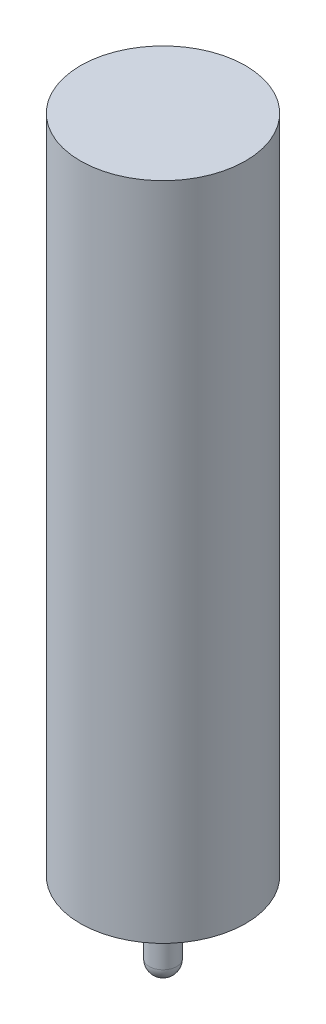
SolidWorks part; units mm, degrees
material "合金鋼 (SS)"
ref_plane "正面" through (0, 0, 0) normal (0, 0, 1) x (1, 0, 0)
ref_plane "平面" through (0, 0, 0) normal (0, 1, 0) x (1, 0, 0)
ref_plane "右側面" through (0, 0, 0) normal (1, 0, 0) x (0, 0, -1)
sketch "ｽｹｯﾁ1" plane through (0, 0, 0) normal (0, 1, 0) x (1, 0, 0)
  circle A0 centre (0, 0) radius 1.5
extrude "ﾎﾞｽ - 押し出し2" add sketch "ｽｹｯﾁ1" along normal blind 24
sketch "ｽｹｯﾁ3" plane through (0, 0, 0) normal (0, -1, 0) x (1, 0, 0)
  circle A0 centre (0, 0) radius 0.5
extrude "ﾎﾞｽ - 押し出し3" add sketch "ｽｹｯﾁ3" along normal blind 3.1
fillet "ﾌｨﾚｯﾄ1" radius 0.5 1 edges at (0, -3.1, -0.5)
sketch "ｽｹｯﾁ4" plane through (0, 24, 0) normal (0, 1, 0) x (1, 0, 0)
  circle A0 centre (0, 0) radius 3
extrude "ﾎﾞｽ - 押し出し4" add sketch "ｽｹｯﾁ4" against normal up to surface (24 mm away) up to face at (0, 0, 0.5)
